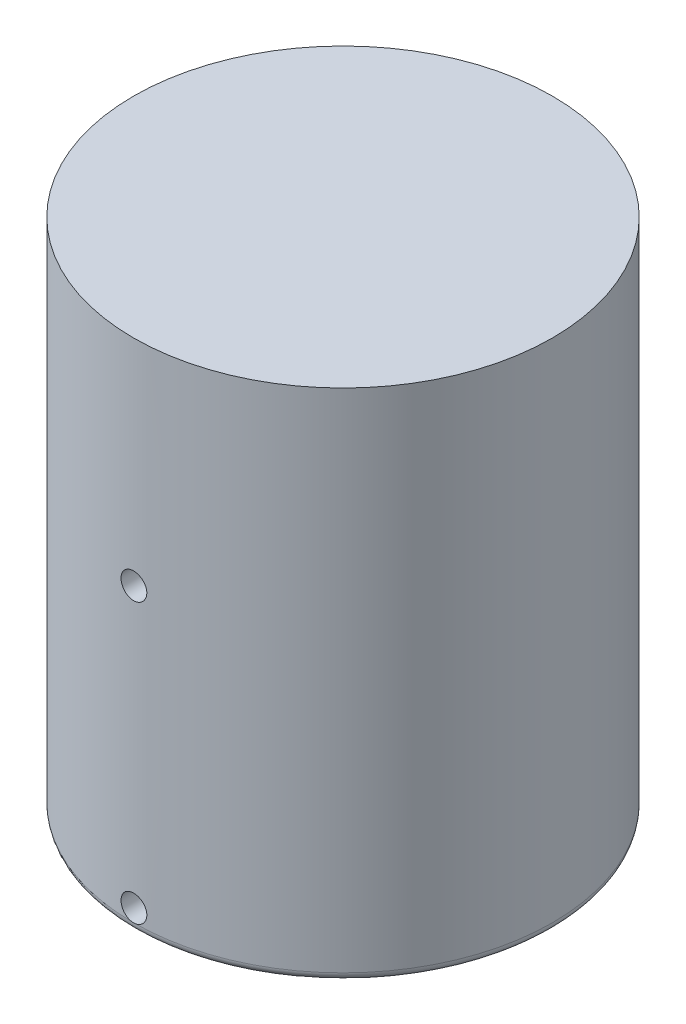
SolidWorks part; units mm, degrees
ref_plane "Front" through (0, 0, 0) normal (0, 0, 1) x (1, 0, 0)
ref_plane "Top" through (0, 0, 0) normal (0, 1, 0) x (1, 0, 0)
ref_plane "Right" through (0, 0, 0) normal (1, 0, 0) x (0, 0, -1)
sketch "Sketch1" plane through (0, 0, 0) normal (0, 1, 0) x (1, 0, 0)
  circle A0 centre (0, 0) radius 6.1976
extrude "Boss-Extrude1" add sketch "Sketch1" along normal blind 15.24
sketch "Sketch2" plane through (0, 0, 0) normal (0, -1, 0) x (1, 0, 0)
  circle A0 centre (0, 0) radius 4.7625
extrude "Cut-Extrude1" cut sketch "Sketch2" against normal blind 0.635
hole_wizard "1/4-20 Tapped Hole1" positions "Sketch3" profile "Sketch5" tap size "1/4-20" standard "ANSI Inch"
sketch "Sketch3" plane through (0, 0.635, 0) normal (0, -1, 0) x (-1, 0, 0)
  point P0 (0, 0)
cosmetic thread "Hole Thread1" parameters "D1"=6.35, "D2"=6.35
sketch "Sketch5" plane through (0, 0.635, 0) normal (1, 0, 0) x (0, 0, -1)
  line L0 (0, 0) -> (0, 9.1538)
  line L1 (0, 9.1538) -> (2.5527, 7.62)
  line L2 (2.5527, 7.62) -> (2.5527, 0.635)
  line L3 (2.5527, 0.635) -> (3.1877, 0)
  line L5 (3.1877, 0) -> (0, 0)
  line L6 (-2.5527, 0.635) -> (-3.1877, 0) construction
  line L10 (0, 9.1538) -> (-2.5527, 7.62) construction
  line L11 (0, -6.35) -> (0, 107.95) construction
  dimension "Tap Drill Dia." = 5.1054
  dimension "Tap Drill Depth" = 7.62
  dimension "Near C'Sink Dia." = 6.3754
  dimension "Near C'Sink Angle" = 90
  dimension "Drill Angle" = 118
fillet "Fillet4" radius 0.254 1 edges at (0, 0, 6.1976)
sketch "Sketch7" plane through (0, 0, 0) normal (0, 0, 1) x (1, 0, 0)
  circle A0 centre (0, 0.635) radius 0.381
  circle A1 centre (0, 8.89) radius 0.381
extrude "Cut-Extrude2" cut sketch "Sketch7" against normal through all both and the other way through all
